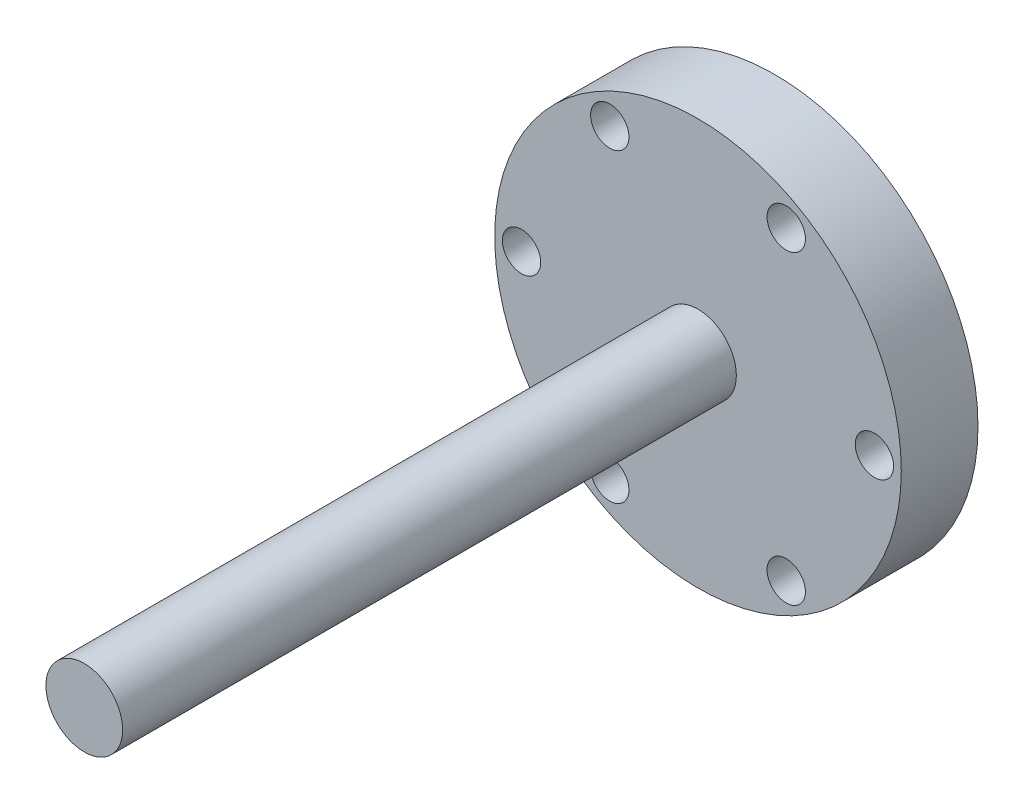
SolidWorks part; units mm, degrees
ref_plane "Front Plane" through (0, 0, 0) normal (0, 0, 1) x (1, 0, 0)
ref_plane "Top Plane" through (0, 0, 0) normal (0, 1, 0) x (1, 0, 0)
ref_plane "Right Plane" through (0, 0, 0) normal (1, 0, 0) x (0, 0, -1)
sketch "Sketch1" plane through (0, 0, 0) normal (0, 0, 1) x (1, 0, 0)
  line L0 (0, 0) -> (23, 0) construction
  line L1 (0, 0) -> (11.5, 19.9186) construction
  line L2 (0, 0) -> (-11.5, 19.9186) construction
  line L3 (0, 0) -> (-23, 0) construction
  line L4 (0, 0) -> (-11.5, -19.9186) construction
  line L5 (0, 0) -> (11.5, -19.9186) construction
  circle A0 centre (0, 0) radius 26.5
  circle A1 centre (23, 0) radius 2.5
  circle A2 centre (11.5, 19.9186) radius 2.5
  circle A3 centre (-11.5, 19.9186) radius 2.5
  circle A4 centre (-23, 0) radius 2.5
  circle A5 centre (-11.5, -19.9186) radius 2.5
  circle A6 centre (11.5, -19.9186) radius 2.5
  dimension "D1" = 53
  dimension "D3" = 5
  dimension "D14" = 5
  dimension "D15" = 5
  dimension "D16" = 5
  dimension "D17" = 5
  dimension "D18" = 5
  dimension "D2" = 23
  dimension "D4" = 23
  dimension "D5" = 23
  dimension "D6" = 23
  dimension "D7" = 23
  dimension "D8" = 23
  dimension "D9" = 60
  dimension "D10" = 120
  dimension "D11" = 180
  dimension "D12" = 60
  dimension "D13" = 120
extrude "Boss-Extrude1" add sketch "Sketch1" along normal blind 10
sketch "Sketch2" plane through (0, 0, 10) normal (0, 0, 1) x (1, 0, 0)
  circle A0 centre (0, 0) radius 5
  dimension "D1" = 10
extrude "Boss-Extrude2" add sketch "Sketch2" along normal blind 80
